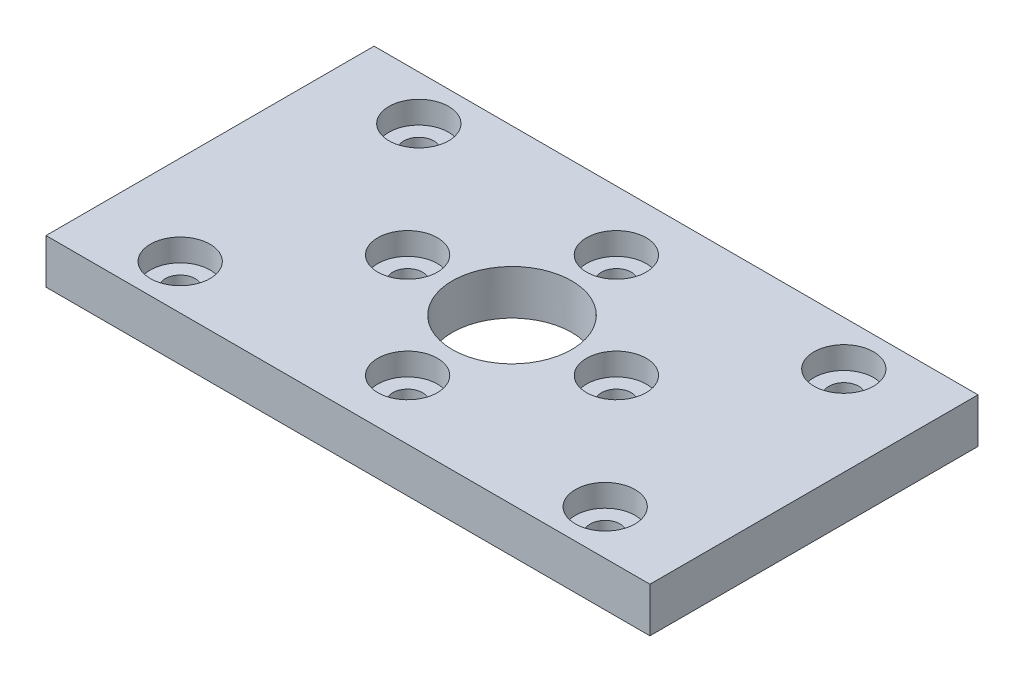
SolidWorks part; units mm, degrees
ref_plane "Front Plane" through (0, 0, 0) normal (0, 0, 1) x (1, 0, 0)
ref_plane "Top Plane" through (0, 0, 0) normal (0, 1, 0) x (1, 0, 0)
ref_plane "Right Plane" through (0, 0, 0) normal (1, 0, 0) x (0, 0, -1)
sketch "Sketch1" plane through (0, 0, 0) normal (0, 1, 0) x (1, 0, 0)
  line L1 (-20.25, -11) -> (20.25, -11)
  line L2 (-20.25, -11) -> (-20.25, 11)
  line L3 (-20.25, 11) -> (20.25, 11)
  line L4 (20.25, -11) -> (20.25, 11)
  line L5 (-20.25, -11) -> (20.25, 11) construction
  line L6 (-20.25, 11) -> (20.25, -11) construction
  point P0 (0, 0)
  dimension "D1" = 40.5
  dimension "D2" = 22
extrude "Boss-Extrude1" add sketch "Sketch1" along normal blind 3
sketch "Sketch2" plane through (0, 3, 0) normal (0, 1, 0) x (1, 0, 0)
  line L0 (-20.25, 11) -> (-20.25, -11) construction
  line L1 (20.25, -11) -> (20.25, 11) construction
  line L2 (20.25, 11) -> (-20.25, 11) construction
  line L3 (-20.25, -11) -> (20.25, -11) construction
  circle A0 centre (-14.25, 8) radius 1
  circle A1 centre (-14.25, -8) radius 1
  circle A2 centre (14.25, -8) radius 1
  circle A3 centre (14.25, 8) radius 1
  dimension "D9" = 2
  dimension "D10" = 2
  dimension "D11" = 2
  dimension "D12" = 2
  dimension "D1" = 6
  dimension "D2" = 6
  dimension "D3" = 6
  dimension "D4" = 6
  dimension "D5" = 3
  dimension "D6" = 3
  dimension "D7" = 3
  dimension "D8" = 3
extrude "Cut-Extrude1" cut sketch "Sketch2" against normal blind 10
sketch "Sketch3" plane through (0, 3, 0) normal (0, 1, 0) x (1, 0, 0)
  circle A0 centre (0, 0) radius 4
  dimension "D1" = 8
extrude "Cut-Extrude2" cut sketch "Sketch3" against normal blind 10
sketch "Sketch4" plane through (0, 3, 0) normal (0, 1, 0) x (1, 0, 0)
  circle A0 centre (0, 0) radius 7 construction
  circle A1 centre (0, 7) radius 1
  circle A2 centre (7, 0) radius 1
  circle A3 centre (0, -7) radius 1
  circle A4 centre (-7, 0) radius 1
  point P14 (0, 0)
  dimension "D1" = 14
  dimension "D2" = 2
  dimension "D3" = 4
extrude "Cut-Extrude3" cut sketch "Sketch4" against normal blind 10
sketch "Sketch5" plane through (0, 3, 0) normal (0, 1, 0) x (1, 0, 0)
  line L0 (-26.3744, 0) -> (24.612, 0) construction
  circle A0 centre (14.25, 8) radius 2
  circle A1 centre (0, 7) radius 2
  circle A2 centre (-14.25, 8) radius 2
  circle A3 centre (7, 0) radius 2
  circle A4 centre (-7, 0) radius 2
  circle A5 centre (-14.25, -8) radius 2
  circle A6 centre (0, -7) radius 2
  circle A7 centre (14.25, -8) radius 2
  dimension "D1" = 4
  dimension "D2" = 4
  dimension "D3" = 4
  dimension "D4" = 4
  dimension "D5" = 4
extrude "Cut-Extrude4" cut sketch "Sketch5" against normal blind 1.5
sketch "Sketch6" plane through (0, 3, 0) normal (0, 1, 0) x (1, 0, 0)
  point P0 (0, 0)
